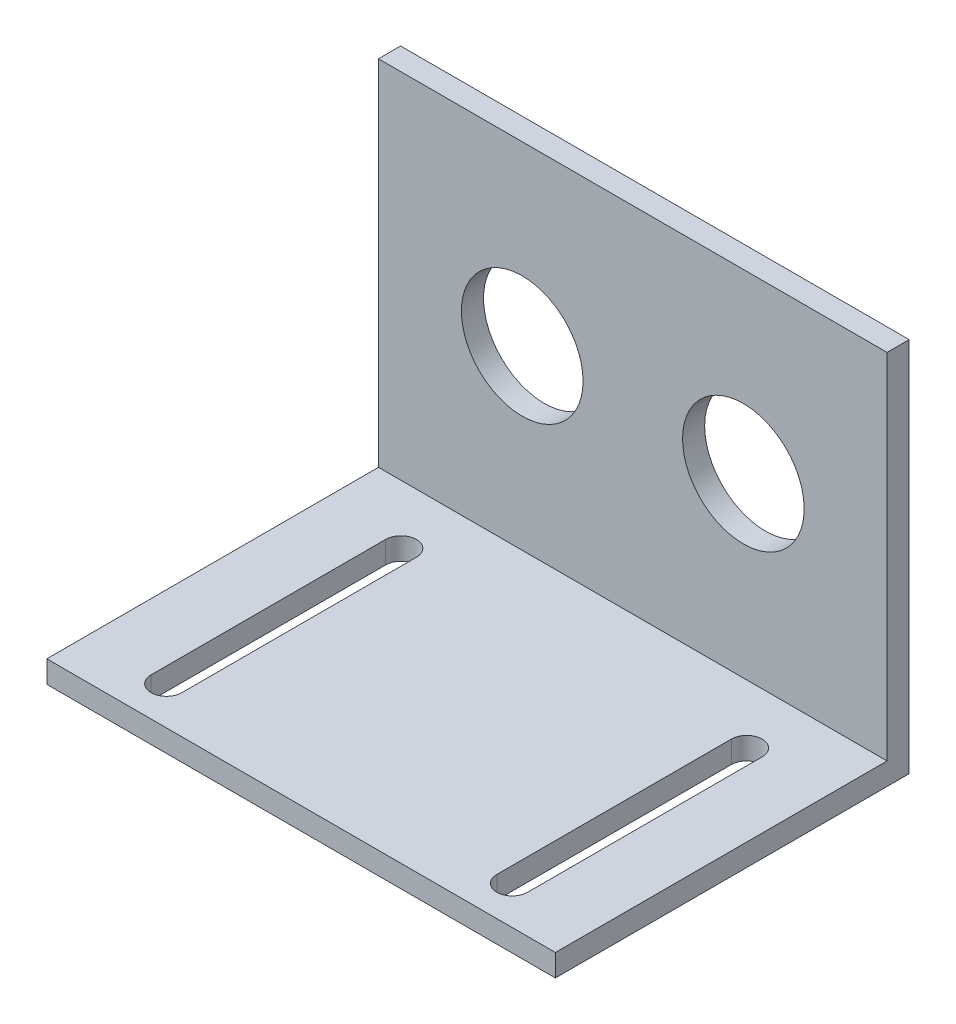
SolidWorks part; units mm, degrees
ref_plane "前视基准面" through (0, 0, 0) normal (0, 0, 1) x (1, 0, 0)
ref_plane "上视基准面" through (0, 0, 0) normal (0, 1, 0) x (1, 0, 0)
ref_plane "右视基准面" through (0, 0, 0) normal (1, 0, 0) x (0, 0, -1)
sketch "草图1" plane through (0, 0, 0) normal (0, 0, 1) x (1, 0, 0)
  line L0 (-30.2063, 34) -> (-30.2063, 0)
  line L1 (-30.2063, 0) -> (15.7937, 0)
  line L2 (15.7937, 0) -> (15.7937, 34)
  line L3 (15.7937, 34) -> (-30.2063, 34)
  dimension "D1" = 34
  dimension "D2" = 46
extrude "凸台-拉伸1" add sketch "草图1" along normal blind 2
sketch "草图2" plane through (0, 0, 2) normal (0, 0, 1) x (1, 0, 0)
  line L0 (-30.2063, 0) -> (-30.2063, 2)
  line L1 (-30.2063, 34) -> (-30.2063, 0) construction
  line L2 (-30.2063, 2) -> (15.7937, 2)
  line L3 (15.7937, 0) -> (15.7937, 34) construction
  line L4 (15.7937, 2) -> (15.7937, 0)
  line L5 (15.7937, 0) -> (-30.2063, 0)
  dimension "D1" = 2
extrude "凸台-拉伸2" add sketch "草图2" along normal blind 30
sketch "草图3" plane through (0, 0, 2) normal (0, 0, 1) x (1, 0, 0)
  line L0 (-30.2063, 34) -> (-30.2063, 18) construction
  line L1 (-7.2063, 2) -> (-7.2063, 34) construction
  line L2 (-30.2063, 34) -> (-30.2063, 2) construction
  line L3 (-30.2063, 18) -> (-17.2063, 18) construction
  line L4 (15.7937, 2) -> (-30.2063, 2) construction
  line L5 (15.7937, 34) -> (-30.2063, 34) construction
  line L6 (15.7937, 18) -> (2.7937, 18) construction
  line L7 (15.7937, 34) -> (15.7937, 18) construction
  circle A0 centre (-17.2063, 18) radius 5.5
  circle A1 centre (2.7937, 18) radius 5.5
  dimension "D3" = 11
  dimension "D1" = 16
  dimension "D2" = 13
extrude "切除-拉伸1" cut sketch "草图3" against normal blind 2
sketch "草图4" plane through (0, 2, 0) normal (0, 1, 0) x (1, 0, 0)
  line L0 (-7.2063, -2) -> (-7.2063, -32) construction
  line L2 (-24.2357, -7.3283) -> (-24.2357, -28.54)
  line L4 (-21.4476, -7.3283) -> (-21.4476, -28.54)
  line L5 (15.7937, -2) -> (-30.2063, -2) construction
  line L6 (15.7937, -32) -> (-30.2063, -32) construction
  line L7 (7.035, -7.3283) -> (7.035, -28.54)
  line L8 (9.8231, -7.3283) -> (9.8231, -28.54)
  arc A0 (-21.4476, -7.3283) -> (-24.2357, -7.3283) centre (-22.8416, -7.3283) ccw
  arc A1 (-24.2357, -28.54) -> (-21.4476, -28.54) centre (-22.8416, -28.54) ccw
  arc A2 (9.8231, -28.54) -> (7.035, -28.54) centre (8.4291, -28.54) cw
  arc A3 (7.035, -7.3283) -> (9.8231, -7.3283) centre (8.4291, -7.3283) cw
extrude "切除-拉伸2" cut sketch "草图4" against normal blind 2
